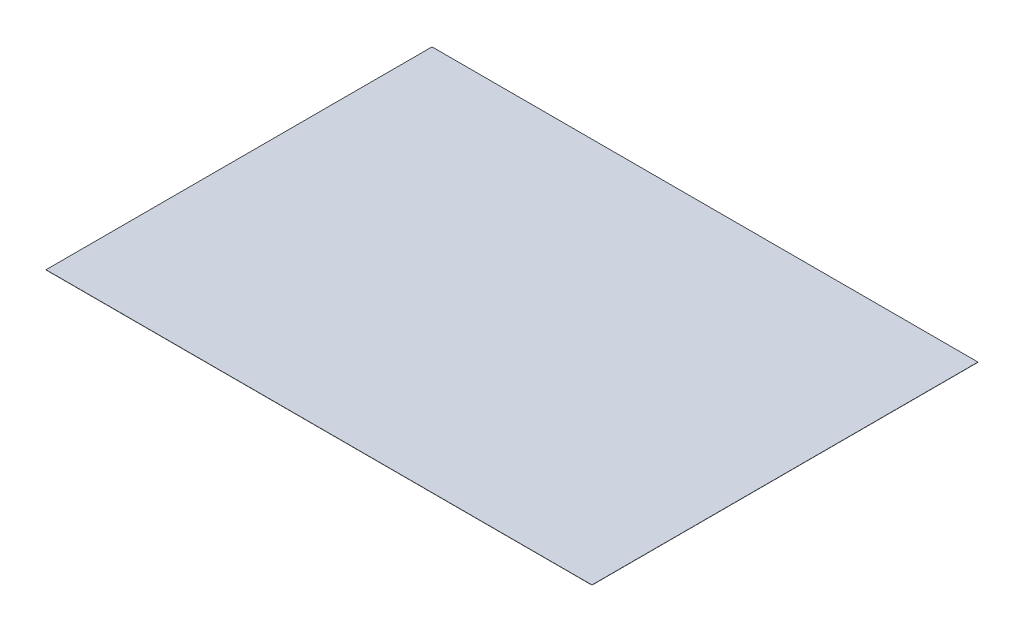
SolidWorks part; units mm, degrees
ref_plane "前视基准面" through (0, 0, 0) normal (0, 0, 1) x (1, 0, 0)
ref_plane "上视基准面" through (0, 0, 0) normal (0, 1, 0) x (1, 0, 0)
ref_plane "右视基准面" through (0, 0, 0) normal (1, 0, 0) x (0, 0, -1)
sketch "草图1" plane through (0, 0, 0) normal (0, 1, 0) x (1, 0, 0)
  line L1 (0, 0) -> (297, 0)
  line L2 (0, 0) -> (0, 210)
  line L3 (0, 210) -> (297, 210)
  line L4 (297, 0) -> (297, 210)
  dimension "D1" = 210
  dimension "D2" = 297
extrude "凸台-拉伸1" add sketch "草图1" along normal blind 0.1
